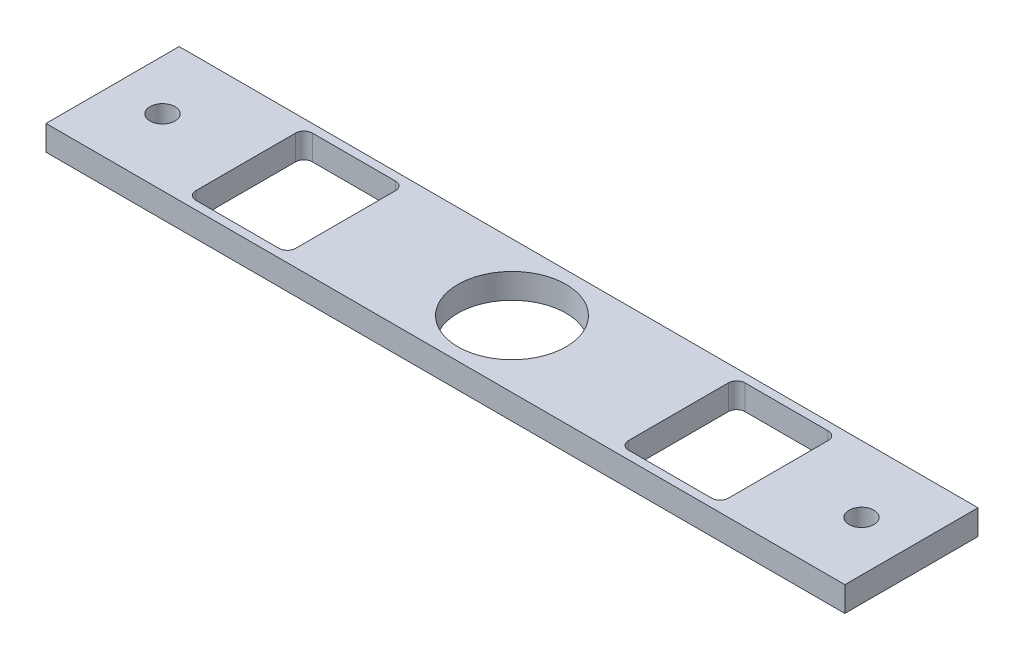
SolidWorks part; units mm, degrees
material "6061-T6 (SS)"
ref_plane "Front Plane" through (0, 0, 0) normal (0, 0, 1) x (1, 0, 0)
ref_plane "Top Plane" through (0, 0, 0) normal (0, 1, 0) x (1, 0, 0)
ref_plane "Right Plane" through (0, 0, 0) normal (1, 0, 0) x (0, 0, -1)
sketch "Sketch1" plane through (0, 0, 0) normal (0, 1, 0) x (1, 0, 0)
  line L1 (-152.4, 25.4) -> (152.4, 25.4)
  line L2 (-152.4, 25.4) -> (-152.4, -25.4)
  line L3 (-152.4, -25.4) -> (152.4, -25.4)
  line L4 (152.4, 25.4) -> (152.4, -25.4)
  line L5 (-152.4, 25.4) -> (152.4, -25.4) construction
  line L6 (-152.4, -25.4) -> (152.4, 25.4) construction
  point P0 (0, 0)
  dimension "D1" = 50.8
  dimension "D2" = 304.8
extrude "Boss-Extrude1" add sketch "Sketch1" along normal blind 9.525
sketch "Sketch2" plane through (0, 9.525, 0) normal (0, 1, 0) x (1, 0, 0)
  circle A0 centre (0, 0) radius 20.6375
  dimension "D1" = 41.275
extrude "Cut-Extrude1" cut sketch "Sketch2" against normal through all
sketch "Sketch3" plane through (0, 9.525, 0) normal (0, 1, 0) x (1, 0, 0)
  line L0 (152.4, -25.4) -> (152.4, 25.4) construction
  circle A0 centre (133.35, 0) radius 4.7625
  dimension "D1" = 9.525
  dimension "D2" = 19.05
extrude "Cut-Extrude2" cut sketch "Sketch3" against normal through all
sketch "Sketch4" plane through (0, 9.525, 0) normal (0, 1, 0) x (1, 0, 0)
  line L1 (-63.5, 22.225) -> (0, 0) construction
  line L2 (-101.6, 22.225) -> (-63.5, 22.225)
  line L3 (-101.6, 22.225) -> (-101.6, -22.225)
  line L4 (-101.6, -22.225) -> (-63.5, -22.225)
  line L5 (-63.5, 22.225) -> (-63.5, -22.225)
  line L6 (-101.6, 22.225) -> (-63.5, -22.225) construction
  line L7 (-101.6, -22.225) -> (-63.5, 22.225) construction
  line L8 (63.5, 22.225) -> (101.6, 22.225)
  line L11 (63.5, 22.225) -> (63.5, -22.225)
  line L12 (63.5, -22.225) -> (101.6, -22.225)
  line L13 (101.6, 22.225) -> (101.6, -22.225)
  line L14 (63.5, 22.225) -> (101.6, -22.225) construction
  line L15 (63.5, -22.225) -> (101.6, 22.225) construction
  line L16 (0, 0) -> (-63.5, -22.225) construction
  line L17 (63.5, 22.225) -> (0, 0) construction
  line L18 (0, 0) -> (63.5, -22.225) construction
  line L19 (152.4, 25.4) -> (-152.4, 25.4) construction
  line L20 (-152.4, 25.4) -> (-152.4, -25.4) construction
  point P0 (-82.55, 0)
  point P5 (82.55, 0)
  dimension "D1" = 38.1
  dimension "D2" = 3.175
  dimension "D3" = 50.8
extrude "Cut-Extrude3" cut sketch "Sketch4" against normal through all
sketch "Sketch5" plane through (0, 9.525, 0) normal (0, 1, 0) x (1, 0, 0)
  line L0 (-152.4, 25.4) -> (-152.4, -25.4) construction
  circle A0 centre (-133.35, 0) radius 4.7625
  dimension "D1" = 9.525
  dimension "D2" = 19.05
extrude "Cut-Extrude4" cut sketch "Sketch5" against normal through all
fillet "Fillet1" radius 3.175 8 edges at (63.5, 4.7625, -22.225) (101.6, 4.7625, 22.225) (101.6, 4.7625, -22.225) (63.5, 4.7625, 22.225) (-101.6, 4.7625, 22.225) (-63.5, 4.7625, 22.225) (-63.5, 4.7625, -22.225) (-101.6, 4.7625, -22.225)
